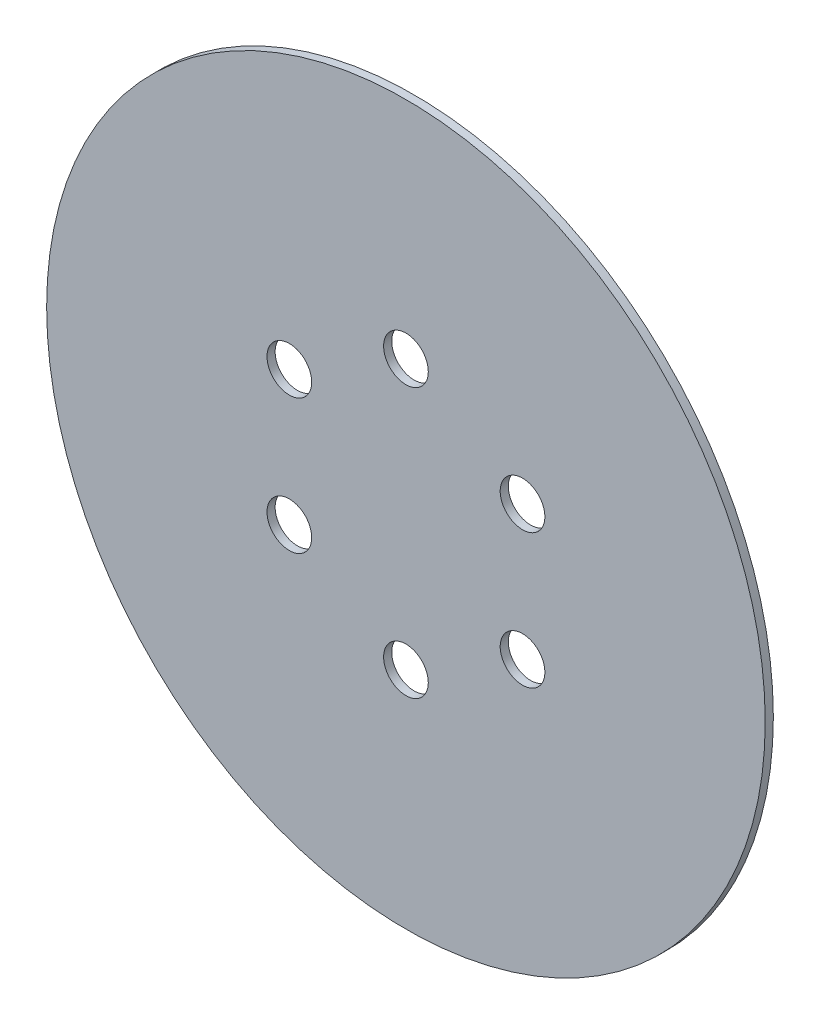
SolidWorks part; units mm, degrees
ref_plane "Front Plane" through (0, 0, 0) normal (0, 0, 1) x (1, 0, 0)
ref_plane "Top Plane" through (0, 0, 0) normal (0, 1, 0) x (1, 0, 0)
ref_plane "Right Plane" through (0, 0, 0) normal (1, 0, 0) x (0, 0, -1)
sketch "Sketch1" plane through (0, 0, 0) normal (0, 0, 1) x (1, 0, 0)
  circle A1 centre (0, 1.0493) radius 44.22
  circle A3 centre (0, 17.6193) radius 2.75
  circle A4 centre (14.35, 9.3343) radius 2.75
  circle A5 centre (14.35, -7.2357) radius 2.75
  circle A6 centre (0, -15.5207) radius 2.75
  circle A7 centre (-14.35, -7.2357) radius 2.75
  circle A8 centre (-14.35, 9.3343) radius 2.75
  dimension "D2" = 88.44
extrude "Boss-Extrude1" add sketch "Sketch1" along normal blind 1
